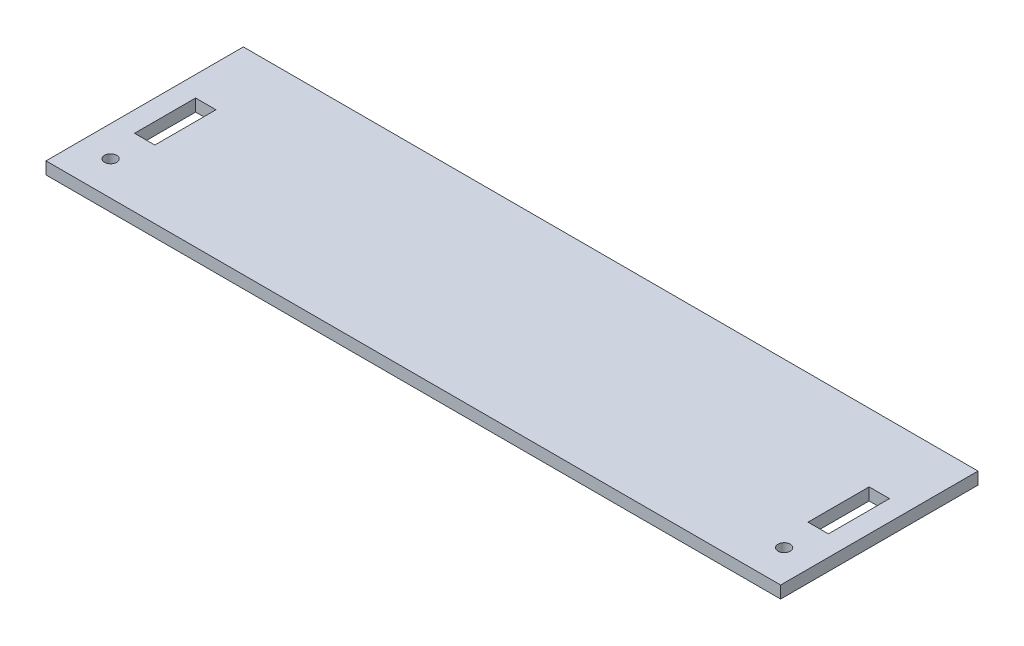
SolidWorks part; units mm, degrees
material "PMMA"
ref_plane "Front Plane" through (0, 0, 0) normal (0, 0, 1) x (1, 0, 0)
ref_plane "Top Plane" through (0, 0, 0) normal (0, 1, 0) x (1, 0, 0)
ref_plane "Right Plane" through (0, 0, 0) normal (1, 0, 0) x (0, 0, -1)
sketch "Schizzo1" plane through (0, 0, 0) normal (0, 1, 0) x (1, 0, 0)
  line L0 (-90.17, -24.225) -> (90.17, 24.225) construction
  line L1 (-90.17, 24.225) -> (90.17, 24.225)
  line L2 (-90.17, 24.225) -> (-90.17, -24.225)
  line L3 (-90.17, -24.225) -> (90.17, -24.225)
  line L4 (90.17, 24.225) -> (90.17, -24.225)
  point P4 (0, 0)
  dimension "D1" = 48.45
  dimension "D2" = 180.34
extrude "Estrusione-Estrusione1" add sketch "Schizzo1" along normal blind 3
sketch "Schizzo2" plane through (0, 0, 0) normal (0, 1, 0) x (1, 0, 0)
  line L0 (-90.17, 0) -> (90.17, 0) construction
  line L1 (-85.17, 7.5) -> (-80.17, 7.5)
  line L2 (-85.17, 7.5) -> (-85.17, -7.5)
  line L3 (-85.17, -7.5) -> (-80.17, -7.5)
  line L4 (-80.17, 7.5) -> (-80.17, -7.5)
  line L5 (-90.17, 24.225) -> (-90.17, -24.225) construction
  line L6 (90.17, -24.225) -> (90.17, 24.225) construction
  line L7 (0, -24.225) -> (0, 24.225) construction
  line L8 (-90.17, -24.225) -> (90.17, -24.225) construction
  line L9 (90.17, 24.225) -> (-90.17, 24.225) construction
  line L10 (85.17, 7.5) -> (80.17, 7.5)
  line L11 (85.17, 7.5) -> (85.17, -7.5)
  line L12 (85.17, -7.5) -> (80.17, -7.5)
  line L13 (80.17, 7.5) -> (80.17, -7.5)
  line L22 (-82.67, -7.5) -> (-82.67, -24.225) construction
  circle A0 centre (-82.67, -15.8625) radius 1.5
  circle A1 centre (82.67, -15.8625) radius 1.5
  point P6 (-80.17, 0)
  point P34 (-82.67, -15.8625)
  dimension "D3" = 3
  dimension "D1" = 15
  dimension "D2" = 5
  dimension "D4" = 5
extrude "Taglio-Estrusione1" cut sketch "Schizzo2" along direction (0, 1, 0) on the side of the normal through all
equation "\"Thickness5\"= 5"
equation "\"D1@Estrusione-Estrusione1\"=\"Thickness3\""
equation "\"D2@Schizzo2\"=\"Thickness5\""
equation "\"Thickness3\"= 3"
